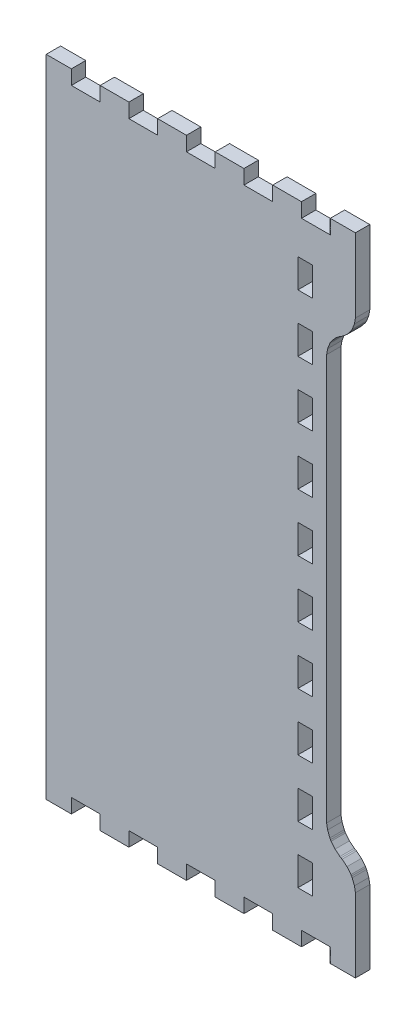
SolidWorks part; units mm, degrees
ref_plane "Front Plane" through (0, 0, 0) normal (0, 0, 1) x (1, 0, 0)
ref_plane "Top Plane" through (0, 0, 0) normal (0, 1, 0) x (1, 0, 0)
ref_plane "Right Plane" through (0, 0, 0) normal (1, 0, 0) x (0, 0, -1)
sketch "Model" plane through (0, 0, 0) normal (0, 0, 1) x (1, 0, 0)
  line L725 (1156.4315, 23.2006) -> (1166.4239, 23.2006)
  line L726 (1166.4239, 23.2006) -> (1166.4239, 28.9154)
  line L727 (1166.4239, 28.9154) -> (1177.8539, 28.9154)
  line L728 (1177.8539, 28.9154) -> (1177.8539, 23.2006)
  line L729 (1177.8539, 23.2006) -> (1189.2839, 23.2006)
  line L730 (1189.2839, 23.2006) -> (1189.2839, 28.9154)
  line L731 (1189.2839, 28.9154) -> (1200.7139, 28.9154)
  line L732 (1200.7139, 28.9154) -> (1200.7139, 23.2006)
  line L733 (1200.7139, 23.2006) -> (1212.1439, 23.2006)
  line L734 (1212.1439, 23.2006) -> (1212.1439, 28.9154)
  line L735 (1212.1439, 28.9154) -> (1223.5739, 28.9154)
  line L736 (1223.5739, 28.9154) -> (1223.5739, 23.2006)
  line L737 (1223.5739, 23.2006) -> (1235.0039, 23.2006)
  line L738 (1235.0039, 23.2006) -> (1235.0039, 28.9154)
  line L739 (1235.0039, 28.9154) -> (1246.4339, 28.9154)
  line L740 (1246.4339, 28.9154) -> (1246.4339, 23.2006)
  line L741 (1246.4339, 23.2006) -> (1257.8639, 23.2006)
  line L742 (1257.8639, 23.2006) -> (1257.8639, 28.9154)
  line L743 (1257.8639, 28.9154) -> (1269.2939, 28.9154)
  line L744 (1269.2939, 28.9154) -> (1269.2939, 23.2006)
  line L745 (1269.2939, 23.2006) -> (1279.2888, 23.2006)
  line L746 (1279.2888, 23.2006) -> (1279.2888, 51.7759)
  line L747 (1279.2888, 51.7759) -> (1279.2888, 52.5155)
  line L748 (1279.2888, 52.5155) -> (1278.9002, 54.7342)
  line L749 (1278.9002, 54.7342) -> (1278.0086, 57.0563)
  line L750 (1278.0086, 57.0563) -> (1277.7572, 57.4904)
  line L751 (1277.7572, 57.4904) -> (1277.5082, 57.9257)
  line L752 (1277.5082, 57.9257) -> (1275.9411, 59.8579)
  line L753 (1275.9411, 59.8579) -> (1274.0081, 61.4233)
  line L754 (1274.0081, 61.4233) -> (1273.5738, 61.674)
  line L755 (1273.5738, 61.674) -> (1273.1394, 61.9249)
  line L756 (1273.1394, 61.9249) -> (1271.2065, 63.4919)
  line L757 (1271.2065, 63.4919) -> (1269.6393, 65.4238)
  line L758 (1269.6393, 65.4238) -> (1269.3904, 65.8579)
  line L759 (1269.3904, 65.8579) -> (1269.1389, 66.2932)
  line L760 (1269.1389, 66.2932) -> (1268.2499, 68.6153)
  line L761 (1268.2499, 68.6153) -> (1267.8588, 70.834)
  line L762 (1267.8588, 70.834) -> (1267.8588, 71.5726)
  line L763 (1267.8588, 71.5726) -> (1267.8588, 231.2581)
  line L764 (1267.8588, 231.2581) -> (1267.8588, 231.9983)
  line L765 (1267.8588, 231.9983) -> (1268.2499, 234.217)
  line L766 (1268.2499, 234.217) -> (1269.1389, 236.539)
  line L767 (1269.1389, 236.539) -> (1269.3904, 236.9729)
  line L768 (1269.3904, 236.9729) -> (1269.6393, 237.4085)
  line L769 (1269.6393, 237.4085) -> (1271.2065, 239.3404)
  line L770 (1271.2065, 239.3404) -> (1273.1394, 240.906)
  line L771 (1273.1394, 240.906) -> (1273.5738, 241.1567)
  line L772 (1273.5738, 241.1567) -> (1274.0081, 241.4077)
  line L773 (1274.0081, 241.4077) -> (1275.9411, 242.9744)
  line L774 (1275.9411, 242.9744) -> (1277.5082, 244.9065)
  line L775 (1277.5082, 244.9065) -> (1277.7572, 245.3404)
  line L776 (1277.7572, 245.3404) -> (1278.0086, 245.776)
  line L777 (1278.0086, 245.776) -> (1278.9002, 248.0981)
  line L778 (1278.9002, 248.0981) -> (1279.2888, 250.3167)
  line L779 (1279.2888, 250.3167) -> (1279.2888, 251.0551)
  line L780 (1279.2888, 251.0551) -> (1279.2888, 279.6311)
  line L781 (1279.2888, 279.6311) -> (1269.2939, 279.6311)
  line L782 (1269.2939, 279.6311) -> (1269.2939, 273.9161)
  line L783 (1269.2939, 273.9161) -> (1257.8639, 273.9161)
  line L784 (1257.8639, 273.9161) -> (1257.8639, 279.6311)
  line L785 (1257.8639, 279.6311) -> (1246.4339, 279.6311)
  line L786 (1246.4339, 279.6311) -> (1246.4339, 273.9161)
  line L787 (1246.4339, 273.9161) -> (1235.0039, 273.9161)
  line L788 (1235.0039, 273.9161) -> (1235.0039, 279.6311)
  line L789 (1235.0039, 279.6311) -> (1223.5739, 279.6311)
  line L790 (1223.5739, 279.6311) -> (1223.5739, 273.9161)
  line L791 (1223.5739, 273.9161) -> (1212.1439, 273.9161)
  line L792 (1212.1439, 273.9161) -> (1212.1439, 279.6311)
  line L793 (1212.1439, 279.6311) -> (1200.7139, 279.6311)
  line L794 (1200.7139, 279.6311) -> (1200.7139, 273.9161)
  line L795 (1200.7139, 273.9161) -> (1189.2839, 273.9161)
  line L796 (1189.2839, 273.9161) -> (1189.2839, 279.6311)
  line L797 (1189.2839, 279.6311) -> (1177.8539, 279.6311)
  line L798 (1177.8539, 279.6311) -> (1177.8539, 273.9161)
  line L799 (1177.8539, 273.9161) -> (1166.4239, 273.9161)
  line L800 (1166.4239, 273.9161) -> (1166.4239, 279.6311)
  line L801 (1166.4239, 279.6311) -> (1156.4315, 279.6311)
  line L802 (1156.4315, 279.6311) -> (1156.4315, 23.2006)
  line L803 (1262.1438, 48.5455) -> (1262.1438, 42.8308)
  line L804 (1262.1438, 42.8308) -> (1256.4313, 42.8308)
  line L805 (1256.4313, 42.8308) -> (1256.4313, 54.2605)
  line L806 (1256.4313, 54.2605) -> (1262.1438, 54.2605)
  line L807 (1262.1438, 54.2605) -> (1262.1438, 48.5455)
  line L808 (1262.1438, 71.4057) -> (1262.1438, 65.691)
  line L809 (1262.1438, 65.691) -> (1256.4313, 65.691)
  line L810 (1256.4313, 65.691) -> (1256.4313, 77.1205)
  line L811 (1256.4313, 77.1205) -> (1262.1438, 77.1205)
  line L812 (1262.1438, 77.1205) -> (1262.1438, 71.4057)
  line L813 (1262.1438, 94.266) -> (1262.1438, 88.55)
  line L814 (1262.1438, 88.55) -> (1256.4313, 88.55)
  line L815 (1256.4313, 88.55) -> (1256.4313, 99.9807)
  line L816 (1256.4313, 99.9807) -> (1262.1438, 99.9807)
  line L817 (1262.1438, 99.9807) -> (1262.1438, 94.266)
  line L818 (1262.1438, 117.125) -> (1262.1438, 111.4105)
  line L819 (1262.1438, 111.4105) -> (1256.4313, 111.4105)
  line L820 (1256.4313, 111.4105) -> (1256.4313, 122.841)
  line L821 (1256.4313, 122.841) -> (1262.1438, 122.841)
  line L822 (1262.1438, 122.841) -> (1262.1438, 117.125)
  line L823 (1262.1438, 139.9855) -> (1262.1438, 134.2705)
  line L824 (1262.1438, 134.2705) -> (1256.4313, 134.2705)
  line L825 (1256.4313, 134.2705) -> (1256.4313, 145.7)
  line L826 (1256.4313, 145.7) -> (1262.1438, 145.7)
  line L827 (1262.1438, 145.7) -> (1262.1438, 139.9855)
  line L828 (1262.1438, 162.8455) -> (1262.1438, 157.1308)
  line L829 (1262.1438, 157.1308) -> (1256.4313, 157.1308)
  line L830 (1256.4313, 157.1308) -> (1256.4313, 168.5605)
  line L831 (1256.4313, 168.5605) -> (1262.1438, 168.5605)
  line L832 (1262.1438, 168.5605) -> (1262.1438, 162.8455)
  line L833 (1262.1438, 185.7057) -> (1262.1438, 179.991)
  line L834 (1262.1438, 179.991) -> (1256.4313, 179.991)
  line L835 (1256.4313, 179.991) -> (1256.4313, 191.4205)
  line L836 (1256.4313, 191.4205) -> (1262.1438, 191.4205)
  line L837 (1262.1438, 191.4205) -> (1262.1438, 185.7057)
  line L838 (1262.1438, 208.566) -> (1262.1438, 202.85)
  line L839 (1262.1438, 202.85) -> (1256.4313, 202.85)
  line L840 (1256.4313, 202.85) -> (1256.4313, 214.2807)
  line L841 (1256.4313, 214.2807) -> (1262.1438, 214.2807)
  line L842 (1262.1438, 214.2807) -> (1262.1438, 208.566)
  line L843 (1262.1438, 231.425) -> (1262.1438, 225.7105)
  line L844 (1262.1438, 225.7105) -> (1256.4313, 225.7105)
  line L845 (1256.4313, 225.7105) -> (1256.4313, 237.141)
  line L846 (1256.4313, 237.141) -> (1262.1438, 237.141)
  line L847 (1262.1438, 237.141) -> (1262.1438, 231.425)
  line L848 (1262.1438, 254.2845) -> (1262.1438, 248.5705)
  line L849 (1262.1438, 248.5705) -> (1256.4313, 248.5705)
  line L850 (1256.4313, 248.5705) -> (1256.4313, 259.9995)
  line L851 (1256.4313, 259.9995) -> (1262.1438, 259.9995)
  line L852 (1262.1438, 259.9995) -> (1262.1438, 254.2845)
extrude "Boss-Extrude1" add sketch "Model" along normal blind 5.715
